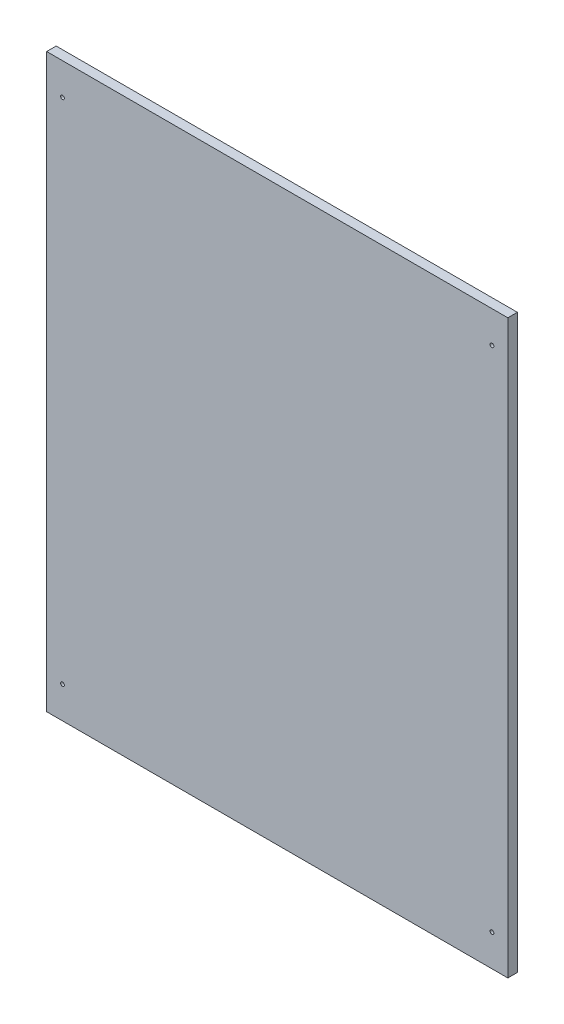
SolidWorks part; units mm, degrees
ref_plane "前视基准面" through (0, 0, 0) normal (0, 0, 1) x (1, 0, 0)
ref_plane "上视基准面" through (0, 0, 0) normal (0, 1, 0) x (1, 0, 0)
ref_plane "右视基准面" through (0, 0, 0) normal (1, 0, 0) x (0, 0, -1)
other "Configuration Table"
sketch "草图1" plane through (0, 0, 0) normal (0, 0, 1) x (1, 0, 0)
  line L0 (0, -835) -> (0, -15) construction
  line L1 (706, -865) -> (0, -865) construction
  line L2 (706, 15) -> (0, 15) construction
  line L3 (706, -835) -> (706, -15) construction
  line L4 (0, -835) -> (0, -15) construction
  line L5 (706, -865) -> (0, -865) construction
  line L6 (706, 15) -> (0, 15) construction
  line L7 (706, -835) -> (706, -15) construction
  line L8 (0, -15) -> (0, 15) construction
  line L9 (706, -15) -> (706, 15) construction
  line L10 (706, -835) -> (706, -865) construction
  line L11 (0, -865) -> (0, -835) construction
  line L12 (-10, -835) -> (-10, -15)
  line L13 (-10, -15) -> (-10, 25)
  line L14 (716, 25) -> (-10, 25)
  line L15 (716, -15) -> (716, 25)
  line L16 (716, -835) -> (716, -15)
  line L17 (716, -835) -> (716, -875)
  line L18 (716, -875) -> (-10, -875)
  line L19 (-10, -875) -> (-10, -835)
  line L20 (0, -425) -> (706, -425) construction
  line L21 (353, 15) -> (353, -865) construction
  circle A0 centre (353, -425) radius 10 construction
  circle A1 centre (483, -425) radius 10 construction
  circle A2 centre (613, -425) radius 10 construction
  circle A3 centre (223, -425) radius 10 construction
  circle A4 centre (93, -425) radius 10 construction
  circle A5 centre (353, -275) radius 10 construction
  circle A6 centre (483, -275) radius 10 construction
  circle A7 centre (613, -275) radius 10 construction
  circle A8 centre (223, -275) radius 10 construction
  circle A9 centre (93, -275) radius 10 construction
  circle A10 centre (353, -125) radius 10 construction
  circle A11 centre (483, -125) radius 10 construction
  circle A12 centre (613, -125) radius 10 construction
  circle A13 centre (223, -125) radius 10 construction
  circle A14 centre (93, -125) radius 10 construction
  circle A15 centre (93, -725) radius 10 construction
  circle A16 centre (223, -725) radius 10 construction
  circle A17 centre (613, -725) radius 10 construction
  circle A18 centre (483, -725) radius 10 construction
  circle A19 centre (353, -725) radius 10 construction
  circle A20 centre (93, -575) radius 10 construction
  circle A21 centre (223, -575) radius 10 construction
  circle A22 centre (613, -575) radius 10 construction
  circle A23 centre (483, -575) radius 10 construction
  circle A24 centre (353, -575) radius 10 construction
  circle A25 centre (15, -25) radius 3
  circle A26 centre (691, -25) radius 3
  circle A27 centre (691, -825) radius 3
  circle A28 centre (15, -825) radius 3
  dimension "D2" = 20
  dimension "D4" = 3
  dimension "D3" = 3
  dimension "D6" = 6
  dimension "D7" = 15
  dimension "D8" = 40
  dimension "D1" = 10
  dimension "D5" = 3
extrude "凸台-拉伸1" add sketch "草图1" along normal blind 15
